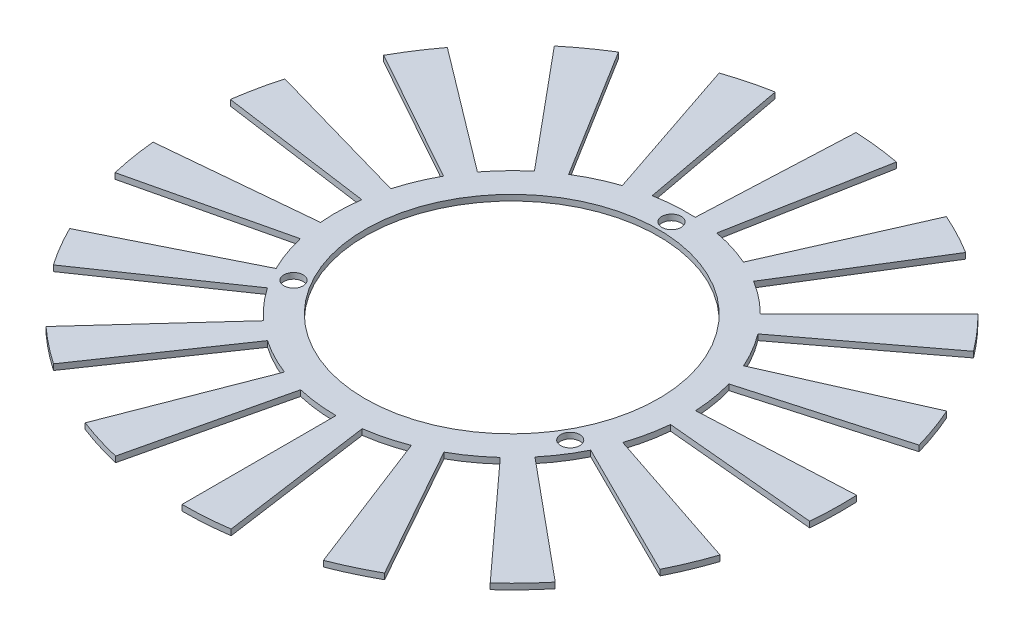
SolidWorks part; units mm, degrees
material "AISI 1010 Steel, hot rolled bar"
ref_plane "Front Plane" through (0, 0, 0) normal (0, 0, 1) x (1, 0, 0)
ref_plane "Top Plane" through (0, 0, 0) normal (0, 1, 0) x (1, 0, 0)
ref_plane "Right Plane" through (0, 0, 0) normal (1, 0, 0) x (0, 0, -1)
sketch "Sketch1" plane through (0, 0, 0) normal (0, 1, 0) x (1, 0, 0)
  circle A0 centre (0, 0) radius 25.25
  dimension "D1" = 50.5
extrude "Extrude-Thin1" add sketch "Sketch1" against normal blind 1 thin
sketch "Sketch2" plane through (0, 0, 0) normal (0, 1, 0) x (1, 0, 0)
  line L0 (0, -30.25) -> (0, 30.25) construction
  line L1 (0, 0) -> (23.8157, -13.75) construction
  line L2 (0, 0) -> (-23.8157, -13.75) construction
  circle A0 centre (0, 27.5) radius 1.65
  circle A1 centre (0, 0) radius 30.25 construction
  circle A4 centre (0, 0) radius 27.5 construction
  circle A7 centre (23.8157, -13.75) radius 1.65
  circle A8 centre (-23.8157, -13.75) radius 1.65
  dimension "D1" = 55
  dimension "D2" = 3.3
  dimension "D3" = 120
  dimension "D4" = 120
extrude "Cut-Extrude3" cut sketch "Sketch2" against normal blind 10
sketch "Sketch5" plane through (0, -1, 0) normal (0, -1, 0) x (1, 0, 0)
  line L0 (0, 0) -> (0, 35.9971) construction
  line L1 (0, 0) -> (4.7467, 33.7749) construction
  line L2 (0, 56.75) -> (0, 30.25)
  line L3 (4.21, 29.9556) -> (7.8981, 56.1977)
  line L4 (20.5005, 52.9178) -> (10.9276, 28.2073)
  line L5 (14.7469, 26.412) -> (27.6657, 49.5497)
  line L6 (38.2322, 41.9388) -> (20.3793, 22.355)
  line L7 (23.2922, 19.3012) -> (43.6969, 36.2097)
  line L8 (50.8005, 25.2957) -> (27.0787, 13.4836)
  line L9 (28.6917, 9.5837) -> (53.8266, 17.9794)
  line L10 (56.5079, 5.2362) -> (30.121, 2.7911)
  line L11 (30.2163, -1.4281) -> (56.6867, -2.6791)
  line L12 (54.5836, -15.5304) -> (29.0952, -8.2783)
  line L13 (27.66, -12.247) -> (51.891, -22.9758)
  line L14 (45.2875, -34.1995) -> (24.14, -18.2297)
  line L15 (21.368, -21.4119) -> (40.0871, -40.1695)
  line L16 (29.875, -48.2498) -> (15.9246, -25.7191)
  line L17 (12.1902, -27.685) -> (22.8692, -51.9381)
  line L18 (10.4278, -55.7837) -> (5.5584, -29.7349)
  line L19 (1.366, -30.2191) -> (2.5627, -56.6921)
  line L20 (-10.4278, -55.7837) -> (-5.5584, -29.7349)
  line L21 (-9.6426, -28.672) -> (-18.0899, -53.7896)
  line L22 (-29.875, -48.2498) -> (-15.9246, -25.7191)
  line L23 (-19.349, -23.2525) -> (-36.2994, -43.6225)
  line L24 (-45.2875, -34.1995) -> (-24.14, -18.2297)
  line L25 (-26.4422, -14.6926) -> (-49.6064, -27.5639)
  line L26 (-54.5836, -15.5304) -> (-29.0952, -8.2783)
  line L27 (-29.9642, -4.1485) -> (-56.2138, -7.7827)
  line L28 (-56.5079, 5.2362) -> (-30.121, 2.7911)
  line L29 (-29.4394, 6.956) -> (-55.2292, 13.0497)
  line L30 (-50.8005, 25.2957) -> (-27.0787, 13.4836)
  line L31 (-24.9386, 17.121) -> (-46.7857, 32.1195)
  line L32 (-38.2322, 41.9388) -> (-20.3793, 22.355)
  line L33 (-17.0697, 24.9737) -> (-32.0234, 46.8515)
  line L34 (-20.5005, 52.9178) -> (-10.9276, 28.2073)
  line L35 (-6.8955, 29.4536) -> (-12.9362, 55.2559)
  circle A0 centre (0, 0) radius 30.25 construction
  arc A1 (4.21, 29.9556) -> (0, 30.25) centre (0, 0) ccw
  arc A2 (7.8981, 56.1977) -> (0, 56.75) centre (0, 0) ccw
  arc A3 (27.6657, 49.5497) -> (20.5005, 52.9178) centre (0, 0) ccw
  arc A4 (14.7469, 26.412) -> (10.9276, 28.2073) centre (0, 0) ccw
  arc A5 (43.6969, 36.2097) -> (38.2322, 41.9388) centre (0, 0) ccw
  arc A6 (23.2922, 19.3012) -> (20.3793, 22.355) centre (0, 0) ccw
  arc A7 (53.8266, 17.9794) -> (50.8005, 25.2957) centre (0, 0) ccw
  arc A8 (28.6917, 9.5837) -> (27.0787, 13.4836) centre (0, 0) ccw
  arc A9 (56.6867, -2.6791) -> (56.5079, 5.2362) centre (0, 0) ccw
  arc A10 (30.2163, -1.4281) -> (30.121, 2.7911) centre (0, 0) ccw
  arc A11 (51.891, -22.9758) -> (54.5836, -15.5304) centre (0, 0) ccw
  arc A12 (27.66, -12.247) -> (29.0952, -8.2783) centre (0, 0) ccw
  arc A13 (40.0871, -40.1695) -> (45.2875, -34.1995) centre (0, 0) ccw
  arc A14 (21.368, -21.4119) -> (24.14, -18.2297) centre (0, 0) ccw
  arc A15 (22.8692, -51.9381) -> (29.875, -48.2498) centre (0, 0) ccw
  arc A16 (12.1902, -27.685) -> (15.9246, -25.7191) centre (0, 0) ccw
  arc A17 (2.5627, -56.6921) -> (10.4278, -55.7837) centre (0, 0) ccw
  arc A18 (1.366, -30.2191) -> (5.5584, -29.7349) centre (0, 0) ccw
  arc A19 (-18.0899, -53.7896) -> (-10.4278, -55.7837) centre (0, 0) ccw
  arc A20 (-9.6426, -28.672) -> (-5.5584, -29.7349) centre (0, 0) ccw
  arc A21 (-36.2994, -43.6225) -> (-29.875, -48.2498) centre (0, 0) ccw
  arc A22 (-19.349, -23.2525) -> (-15.9246, -25.7191) centre (0, 0) ccw
  arc A23 (-49.6064, -27.5639) -> (-45.2875, -34.1995) centre (0, 0) ccw
  arc A24 (-26.4422, -14.6926) -> (-24.14, -18.2297) centre (0, 0) ccw
  arc A25 (-56.2138, -7.7827) -> (-54.5836, -15.5304) centre (0, 0) ccw
  arc A26 (-29.9642, -4.1485) -> (-29.0952, -8.2783) centre (0, 0) ccw
  arc A27 (-55.2292, 13.0497) -> (-56.5079, 5.2362) centre (0, 0) ccw
  arc A28 (-29.4394, 6.956) -> (-30.121, 2.7911) centre (0, 0) ccw
  arc A29 (-46.7857, 32.1195) -> (-50.8005, 25.2957) centre (0, 0) ccw
  arc A30 (-24.9386, 17.121) -> (-27.0787, 13.4836) centre (0, 0) ccw
  arc A31 (-32.0234, 46.8515) -> (-38.2322, 41.9388) centre (0, 0) ccw
  arc A32 (-17.0697, 24.9737) -> (-20.3793, 22.355) centre (0, 0) ccw
  arc A33 (-12.9362, 55.2559) -> (-20.5005, 52.9178) centre (0, 0) ccw
  arc A34 (-6.8955, 29.4536) -> (-10.9276, 28.2073) centre (0, 0) ccw
  point P87 (0, 0)
  dimension "D2" = 26.5
  dimension "D1" = 8
  dimension "D3" = 17
extrude "Boss-Extrude1" add sketch "Sketch5" against normal blind 1
